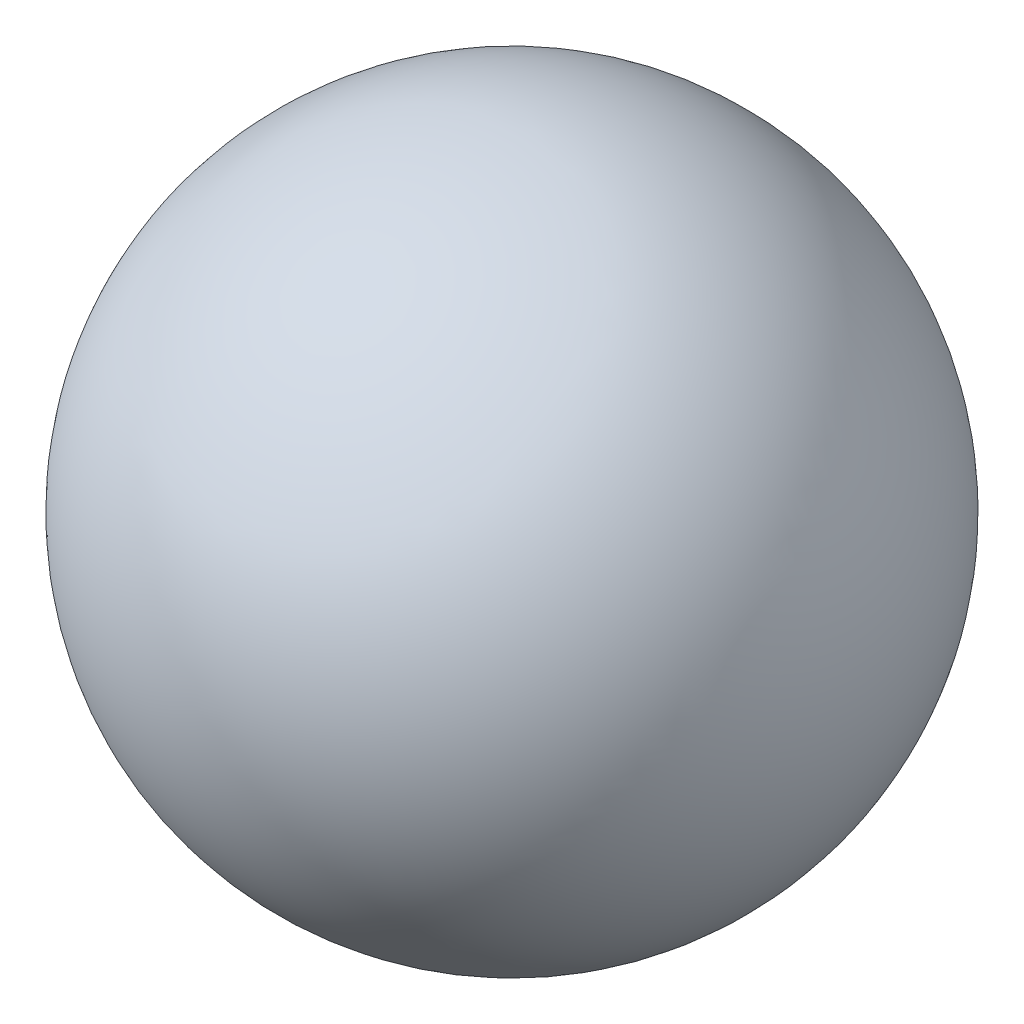
SolidWorks part; units mm, degrees
ref_plane "Front Plane" through (0, 0, 0) normal (0, 0, 1) x (1, 0, 0)
ref_plane "Top Plane" through (0, 0, 0) normal (0, 1, 0) x (1, 0, 0)
ref_plane "Right Plane" through (0, 0, 0) normal (1, 0, 0) x (0, 0, -1)
sketch "Sketch1" plane through (0, 0, 0) normal (0, 0, 1) x (1, 0, 0)
  line L0 (-21.35, 0) -> (21.35, 0)
  arc A0 (21.35, 0) -> (-21.35, 0) centre (0, 0) ccw
  dimension "D1" = 42.7
revolve "Revolve1" add sketch "Sketch1" angle 360 about L0
